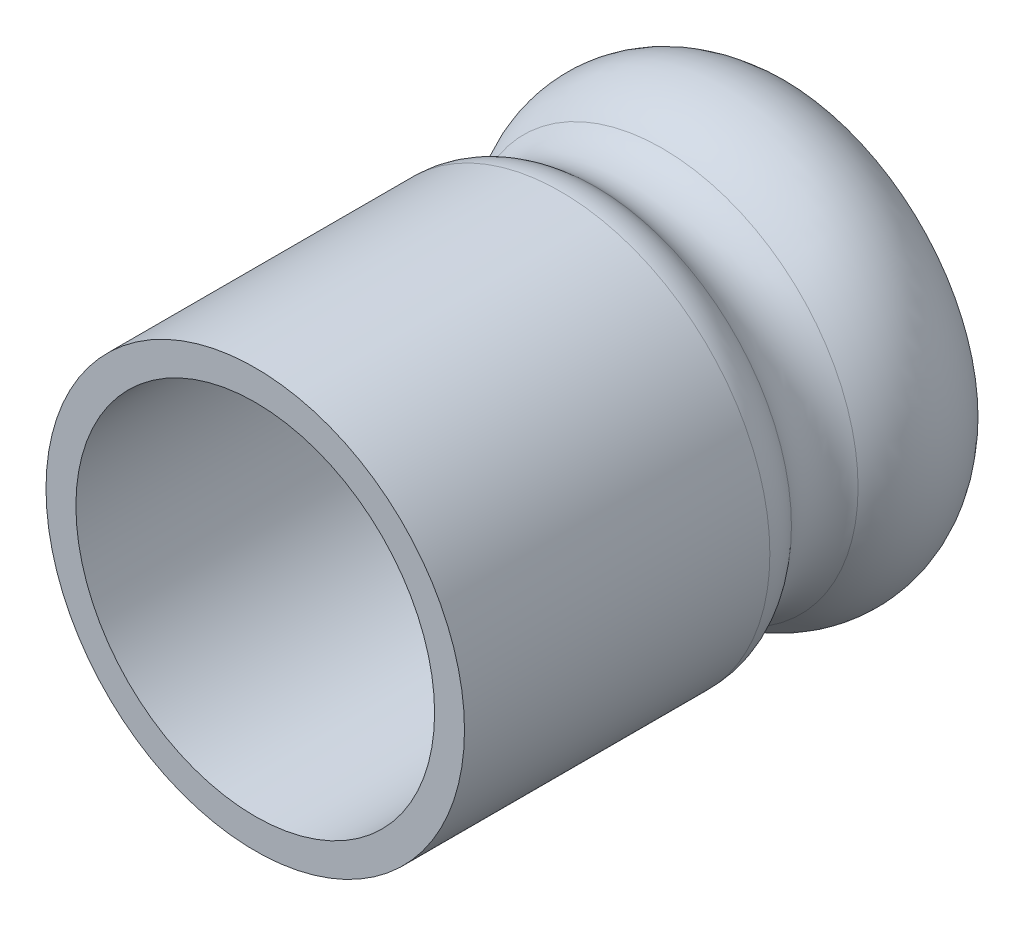
SolidWorks part; units mm, degrees
ref_plane "前视基准面" through (0, 0, 0) normal (0, 0, 1) x (1, 0, 0)
ref_plane "上视基准面" through (0, 0, 0) normal (0, 1, 0) x (1, 0, 0)
ref_plane "右视基准面" through (0, 0, 0) normal (1, 0, 0) x (0, 0, -1)
sketch "草图2" plane through (0, 0, 0) normal (0, 1, 0) x (1, 0, 0)
  line L0 (0, 0) -> (0, 94.0072) construction
  line L1 (0, 0) -> (12, 0)
  line L2 (12, 0) -> (12, 20.432)
  line L3 (10, 35) -> (0, 35)
  line L4 (0, 35) -> (0, 0)
  line L5 (15.5868, 25) -> (10.25, 25) construction
  line L6 (14, 0) -> (14, 20.432)
  line L7 (12, 0) -> (14, 0)
  line L8 (14, -2) -> (14, 20.432) construction
  line L9 (10, 35) -> (14, 35) construction
  line L10 (10, 35) -> (13.0383, 35.3193)
  line L11 (10.3142, 37) -> (-2, 37) construction
  line L13 (-2, 37) -> (-2, -2) construction
  line L14 (-2, -2) -> (14, -2) construction
  arc A0 (12, 20.432) -> (11.616, 21.4342) centre (10.5, 20.432) ccw
  arc A1 (11.616, 21.4342) -> (11.616, 28.5658) centre (15.5868, 25) cw
  arc A2 (11.616, 28.5658) -> (10, 35) centre (8.6399, 31.2383) ccw
  arc A3 (14, 20.432) -> (13.1041, 22.7705) centre (10.5, 20.432) ccw
  arc A4 (13.1041, 22.7705) -> (13.1041, 27.2295) centre (15.5868, 25) cw
  arc A5 (13.1041, 27.2295) -> (13.0383, 35.3193) centre (8.6399, 31.2383) ccw
  arc A6 (13.1041, 27.2295) -> (10.3142, 37) centre (8.6399, 31.2383) ccw construction
  dimension "D4" = 10
  dimension "D5" = 1.5
  dimension "D7" = 4
  dimension "D1" = 20.5
  dimension "D2" = 24
  dimension "D3" = 10
  dimension "D6" = 35
  dimension "D9" = 174
  dimension "D8" = 2
revolve "旋转1" add sketch "草图2" angle 360 about L0
